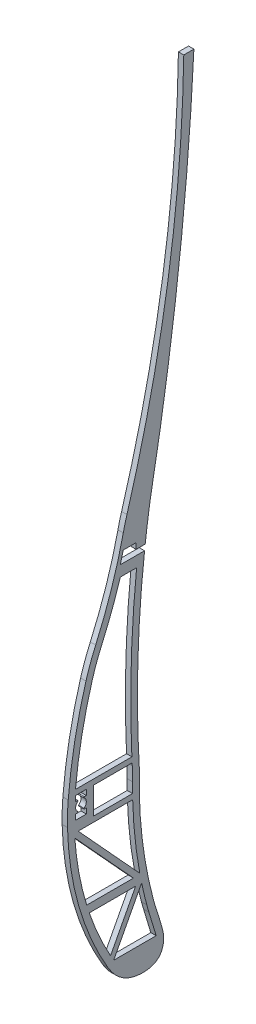
SolidWorks part; units mm, degrees
ref_plane "Front Plane" through (0, 0, 0) normal (0, 0, 1) x (1, 0, 0)
ref_plane "Top Plane" through (0, 0, 0) normal (0, 1, 0) x (1, 0, 0)
ref_plane "Right Plane" through (0, 0, 0) normal (1, 0, 0) x (0, 0, -1)
sketch "rib1" plane through (0, 0, 0) normal (1, 0, 0) x (0, 0, -1)
  line L0 (-71.2313, 530.3957) -> (928.7687, 530.3957) construction
  line L1 (884.1904, 599.9039) -> (887.9745, 599.9039)
  line L2 (856.9345, 370.6416) -> (865.0745, 370.6416)
  line L3 (850.4345, 376.6416) -> (850.4345, 379.6416)
  line L4 (850.4345, 376.6416) -> (850.4345, 373.6416)
  line L5 (840.8063, 376.6416) -> (845.8063, 376.6416) construction
  line L6 (843.8063, 376.6416) -> (843.8063, 374.6416) construction
  line L7 (843.8063, 374.6416) -> (843.8063, 372.6416)
  line L8 (855.8579, 382.6416) -> (843.7452, 382.6416)
  line L9 (855.8579, 382.6416) -> (864.8136, 382.6416)
  line L10 (856.9345, 368.6416) -> (844.7619, 368.6416)
  line L11 (856.9345, 368.6416) -> (865.1127, 368.6416)
  line L12 (866.2204, 340.1291) -> (848.917, 340.1291)
  line L13 (858.3122, 320.8088) -> (858.0269, 320.2668)
  line L14 (848.4203, 343.1291) -> (847.9481, 343.1291)
  line L15 (860.5104, 442.9155) -> (866.5886, 442.9155)
  line L16 (858.0269, 320.2668) -> (873.8862, 320.2668)
  line L17 (855.8579, 318.9992) -> (874.2194, 327.9134) construction
  line L18 (854.766, 321.2482) -> (871.1797, 329.2167) construction
  line L19 (871.1797, 329.2167) -> (873.8862, 320.2668)
  line L20 (843.5049, 367.0528) -> (865.4106, 343.1291)
  line L21 (866.2204, 340.1291) -> (856.8415, 322.3087)
  line L22 (844.7619, 368.6416) -> (867.7752, 343.5082)
  line L23 (868.4574, 340.0851) -> (858.3122, 320.8088)
  line L24 (865.4106, 343.1291) -> (848.4203, 343.1291)
  line L25 (843.8063, 372.6416) -> (847.8063, 372.6416)
  line L26 (856.9345, 370.6416) -> (850.4345, 370.6416)
  line L27 (850.4345, 370.6416) -> (850.4345, 373.6416)
  line L28 (847.8063, 372.6416) -> (847.8063, 374.6416)
  line L29 (855.8579, 380.6416) -> (864.9113, 380.6416)
  line L30 (855.8579, 380.6416) -> (850.4345, 380.6416)
  line L31 (850.4345, 380.6416) -> (850.4345, 379.6416)
  line L32 (843.8063, 374.6416) -> (844.5413, 374.6416)
  line L33 (843.8063, 378.6416) -> (843.8063, 380.6416)
  line L34 (843.8063, 380.6416) -> (847.8063, 380.6416)
  line L35 (843.8063, 378.6416) -> (844.5413, 378.6416)
  line L36 (847.8063, 380.6416) -> (847.8063, 378.6416)
  line L37 (869.548, 446.9155) -> (865.3752, 446.9155)
  line L38 (847.8063, 378.6416) -> (847.0712, 378.6416)
  line L39 (847.8063, 374.6416) -> (847.0712, 374.6416)
  line L40 (870.008, 446.9155) -> (851.9209, 446.9155) construction
  line L41 (869.7893, 448.9413) -> (866.4011, 448.9198)
  line L42 (866.4011, 448.9198) -> (866.4011, 451.1028)
  line L43 (866.4011, 451.1028) -> (861.6081, 451.1028)
  line L44 (861.6081, 451.1028) -> (860.5104, 446.9155)
  line L45 (860.5104, 446.9155) -> (865.3752, 446.9155)
  arc A0 (844.6563, 378.2779) -> (844.6563, 375.0052) centre (845.8063, 376.6416) ccw
  arc A1 (841.0443, 380.5713) -> (847.6718, 415.72) centre (1017.3451, 365.528) cw
  arc A2 (851.2954, 425.5507) -> (861.6081, 456.6454) centre (699.0135, 493.3134) ccw
  arc A3 (862.9829, 461.9026) -> (884.1904, 599.9039) centre (374.0528, 607.6697) ccw
  arc A4 (840.7788, 371.8072) -> (855.8579, 318.9992) centre (950.1899, 374.4922) ccw
  arc A5 (867.6216, 376.9662) -> (872.8022, 332.64) centre (1022.9399, 372.6533) ccw
  arc A6 (867.6216, 376.9662) -> (869.548, 446.9155) centre (1263.0251, 401.0778) cw
  arc A7 (871.9368, 463.9152) -> (887.9745, 599.9039) centre (-120.6116, 649.9108) ccw
  arc A8 (874.2194, 327.9134) -> (872.8022, 332.64) centre (950.104, 353.2418) cw
  arc A9 (841.0443, 380.5713) -> (840.7788, 371.8072) centre (920.7547, 373.7698) ccw
  arc A10 (851.2954, 425.5507) -> (847.6718, 415.72) centre (924.3857, 393.0268) ccw
  arc A11 (862.9829, 461.9026) -> (861.6081, 456.6454) centre (939.6482, 439.046) ccw
  arc A12 (871.4996, 461.3529) -> (871.9368, 463.9152) centre (950.5681, 449.1804) cw
  arc A13 (843.7452, 382.6416) -> (850.0691, 415.0108) centre (1017.3451, 365.528) cw
  arc A14 (853.5794, 424.5344) -> (850.0691, 415.0108) centre (924.3857, 393.0268) ccw
  arc A15 (853.5794, 424.5344) -> (860.5104, 442.9155) centre (699.0135, 493.3134) ccw
  arc A16 (843.5353, 380.3587) -> (850.0691, 415.0108) centre (1017.3451, 365.528) cw construction
  arc A17 (843.5049, 367.0528) -> (847.9481, 343.1291) centre (950.1899, 374.4922) ccw
  arc A18 (865.0721, 374.4641) -> (865.0745, 370.6416) centre (1022.9399, 372.6533) ccw
  arc A19 (864.962, 379.6766) -> (864.9113, 380.6416) centre (1263.0251, 401.0778) cw
  arc A20 (871.1797, 329.2167) -> (870.3865, 331.9962) centre (950.104, 353.2418) cw
  arc A21 (868.4574, 340.0851) -> (870.3865, 331.9962) centre (1022.9399, 372.6533) ccw
  arc A22 (865.3787, 461.1883) -> (886.6901, 599.8658) centre (374.0528, 607.6697) ccw construction
  arc A23 (865.1195, 376.9245) -> (870.3865, 331.9962) centre (1022.9399, 372.6533) ccw construction
  arc A24 (869.4795, 464.3757) -> (885.4776, 600.0277) centre (-120.6116, 649.9108) ccw construction
  arc A25 (843.278, 371.8685) -> (858.0127, 320.2668) centre (950.1899, 374.4922) ccw construction
  arc A26 (853.5794, 424.5344) -> (864.0469, 456.0955) centre (699.0135, 493.3134) ccw construction
  arc A27 (865.3787, 461.1883) -> (864.0469, 456.0955) centre (939.6482, 439.046) ccw construction
  arc A28 (865.1195, 376.9245) -> (869.0287, 461.7333) centre (1263.0251, 401.0778) cw construction
  arc A29 (869.0287, 461.7333) -> (869.4795, 464.3757) centre (950.5681, 449.1804) cw construction
  arc A30 (848.917, 340.1291) -> (856.8415, 322.3087) centre (950.1899, 374.4922) ccw
  arc A31 (865.1127, 368.6416) -> (867.7752, 343.5082) centre (1022.9399, 372.6533) ccw
  arc A32 (864.8136, 382.6416) -> (866.5886, 442.9155) centre (1263.0251, 401.0778) cw
  arc A33 (865.0721, 374.4641) -> (864.962, 379.6766) centre (785.0773, 375.3817) ccw
  arc A34 (844.5413, 378.6416) -> (844.6563, 378.2779) centre (844.5413, 378.4416) cw
  arc A35 (844.6563, 375.0052) -> (844.5413, 374.6416) centre (844.5413, 374.8416) cw
  arc A36 (846.9562, 375.0052) -> (846.9562, 378.2779) centre (845.8063, 376.6416) ccw
  arc A37 (847.0712, 378.6416) -> (846.9562, 378.2779) centre (847.0712, 378.4416) ccw
  arc A38 (847.0712, 374.6416) -> (846.9562, 375.0052) centre (847.0712, 374.8416) cw
  arc A39 (869.7893, 448.9413) -> (871.4996, 461.3529) centre (1263.0251, 401.0778) cw
  arc A40 (867.6216, 376.9662) -> (871.4996, 461.3529) centre (1263.0251, 401.0778) cw construction
  spline S0 degree 3 poles (855.8579, 318.9992) (859.3648, 313.0596) (867.0534, 309.8477) (875.8907, 311.5767) (877.0472, 317.8757) (875.7309, 323.2627) (874.9921, 325.5984) (874.2194, 327.9134) knots 0 0 0 0 0.275026 0.518183 0.708506 0.751927 0.952395 0.952395 0.952395 0.952395
  point P95 (843.8063, 374.6416)
  point P115 (845.8063, 374.6416)
  dimension "D2" = 2.5
  dimension "D3" = 0.2
  dimension "D4" = 0.2
  dimension "D5" = 0.2
  dimension "D6" = 0.2
  dimension "D1" = 1000
sketch "rib2" plane through (0, 0, 0) normal (1, 0, 0) x (0, 0, -1)
  line L0 (-154.4211, 376.6416) -> (49845.5789, 376.6416) construction
  line L1 (-144.1421, 380.6416) -> (49855.8579, 380.6416) construction
  line L2 (-143.0655, 370.6416) -> (49856.9345, 370.6416) construction
  line L3 (782.8933, 343.3859) -> (760.3563, 368.2109)
  line L4 (-143.0655, 368.6416) -> (49856.9345, 368.6416) construction
  line L5 (-144.1421, 382.6416) -> (49855.8579, 382.6416) construction
  line L6 (785.2354, 343.762) -> (762.6647, 368.6416)
  line L7 (764.6298, 343.3859) -> (782.8933, 343.3859)
  line L8 (783.7374, 340.3859) -> (774.2204, 321.3554)
  line L9 (767.5719, 380.6416) -> (767.5719, 370.6416)
  line L10 (767.5719, 370.6416) -> (782.7291, 370.6416)
  line L11 (767.5719, 380.6416) -> (782.2855, 380.6416)
  line L12 (765.5126, 340.3859) -> (783.7374, 340.3859)
  line L13 (762.6647, 368.6416) -> (782.7755, 368.6416)
  line L14 (776.5435, 321.5294) -> (789.8459, 321.5294)
  line L15 (760.7138, 382.6416) -> (782.1585, 382.6416)
  line L16 (770.7866, 427.4918) -> (781.8144, 427.4918)
  line L17 (801.9062, 590.4081) -> (805.115, 590.4081)
  line L18 (757.9166, 376.6416) -> (762.9166, 376.6416) construction
  line L20 (785.9296, 340.298) -> (776.5435, 321.5294)
  circle A0 centre (762.9166, 376.6416) radius 2
  arc A1 (758.9972, 388.4269) -> (758.7602, 360.0657) centre (857.8646, 373.419) ccw
  spline S0 degree 3 poles (758.7602, 360.0657) (759.4545, 354.9126) (761.6392, 342.918) (767.6025, 326.3565) (776.3644, 313.1833) (785.8807, 308.842) (791.3139, 310.6103) (793.0754, 312.9879) (793.3375, 316.1077) (791.0414, 329.6431) (787.956, 341.1966) (785.2042, 359.6207) (785.4538, 372.9971) (783.4315, 397.4301) (785.2476, 420.7625) (783.0535, 455.8097) (784.4694, 464.3867) (788.1328, 479.2935) (793.2428, 503.9805) (802.5401, 542.6054) (805.2587, 572.3941) (805.115, 590.4081) knots 0.028705 0.028705 0.028705 0.028705 0.059247 0.100348 0.1322 0.149146 0.158796 0.160734 0.16766 0.175847 0.234409 0.24607 0.285136 0.310616 0.385264 0.441942 0.454033 0.506165 0.624061 0.777474 1 1 1 1
  spline S1 degree 3 poles (801.9062, 590.4081) (801.6966, 560.1521) (794.9988, 516.4373) (781.9369, 464.9221) (769.955, 434.3358) (762.9603, 410.299) (759.9193, 394.5015) (758.9972, 388.4269) knots 0 0 0 0 0.408823 0.598513 0.719262 0.854061 0.937351 0.937351 0.937351 0.937351
  spline S2 degree 3 poles (760.3563, 368.2109) (760.6455, 365.1083) (761.2971, 359.3998) (762.6856, 351.2079) (763.8909, 346.0643) (764.604, 343.4789) (764.6298, 343.3859) knots 0.01313 0.01313 0.01313 0.01313 0.031626 0.047245 0.062864 0.063447 0.063447 0.063447 0.063447
  spline S3 degree 3 poles (765.5126, 340.3859) (765.9421, 339.0082) (767.2255, 335.1967) (769.2617, 330.2911) (771.6089, 325.6402) (773.0967, 323.06) (774.0043, 321.6748) (774.2204, 321.3554) knots 0.069751 0.069751 0.069751 0.069751 0.078483 0.094102 0.101912 0.109721 0.112105 0.112105 0.112105 0.112105
  spline S5 degree 3 poles (782.7291, 370.6416) (782.7064, 371.5634) (782.6438, 373.8426) (782.4996, 377.1608) (782.3523, 379.5799) (782.2855, 380.6416) knots 0.276245 0.276245 0.276245 0.276245 0.281529 0.289339 0.295445 0.295445 0.295445 0.295445
  spline S6 degree 3 poles (789.8459, 321.5294) (789.8142, 321.6995) (789.7504, 322.0389) (789.4577, 323.5807) (788.9295, 326.2404) (788.1496, 329.9526) (787.3325, 333.724) (786.5882, 337.1579) (786.1256, 339.3494) (785.9296, 340.298) knots 0.178918 0.178918 0.178918 0.178918 0.179894 0.18087 0.187816 0.195625 0.203435 0.211244 0.21717 0.21717 0.21717 0.21717
  spline S7 degree 3 poles (785.2354, 343.762) (784.9117, 345.4358) (784.3695, 348.4126) (783.6834, 352.846) (783.0923, 358.3507) (782.8866, 363.6197) (782.8011, 367.501) (782.7755, 368.6416) knots 0.224345 0.224345 0.224345 0.224345 0.234672 0.242482 0.250291 0.26591 0.27243 0.27243 0.27243 0.27243
  spline S8 degree 3 poles (782.1585, 382.6416) (782.0098, 384.985) (781.5323, 392.7288) (781.6016, 402.5045) (781.8121, 413.0284) (781.8895, 420.0466) (781.8563, 425.0079) (781.8229, 427.0307) (781.8144, 427.4918) knots 0.299279 0.299279 0.299279 0.299279 0.312767 0.344005 0.359624 0.375243 0.383052 0.385336 0.385336 0.385336 0.385336
  spline S9 degree 3 poles (770.7866, 427.4918) (769.4671, 423.3387) (766.9647, 414.7701) (763.3804, 399.8515) (761.5251, 389.0141) (760.7138, 382.6416) knots 0.752168 0.752168 0.752168 0.752168 0.811773 0.874217 0.962264 0.962264 0.962264 0.962264
  point P26 (765.5126, 340.3859)
  point P30 (764.6298, 343.3859)
  point P35 (774.2204, 321.3554)
  point P36 (789.8459, 321.5294)
  point P37 (785.9296, 340.298)
  point P39 (760.3563, 368.2109)
  point P40 (760.0729, 371.4986)
  dimension "D1" = 100
sketch "Sketch5" plane through (0, 0, 0) normal (1, 0, 0) x (0, 0, -1)
  line L0 (-200154.4211, 376.6416) -> (249845.5789, 376.6416) construction
  line L1 (693.317, 322.1015) -> (707.0464, 322.1015)
  line L2 (695.5696, 447.1101) -> (698.3736, 447.1101)
  line L3 (698.6642, 410.7316) -> (681.8197, 410.7316)
  line L4 (698.7261, 405.5878) -> (680.4847, 405.5878)
  line L5 (677.0801, 382.6416) -> (699.3215, 382.6416)
  line L7 (699.7026, 368.6416) -> (679.4803, 368.6416)
  line L8 (-200143.0655, 368.6416) -> (249856.9345, 368.6416) construction
  line L9 (674.1545, 376.6416) -> (679.1545, 376.6416) construction
  line L10 (684.2181, 380.6416) -> (684.2181, 370.6416)
  line L11 (-200144.1421, 380.6416) -> (249855.8579, 380.6416) construction
  line L12 (-200143.0655, 370.6416) -> (249856.9345, 370.6416) construction
  line L13 (684.2181, 370.6416) -> (699.6248, 370.6416)
  line L14 (702.2048, 368.6416) -> (702.335, 365.9116)
  line L15 (699.3639, 380.6416) -> (684.2181, 380.6416)
  line L16 (708.485, 312.754) -> (708.6651, 312.9152)
  line L17 (706.7921, 314.6987) -> (706.9599, 314.7434)
  line L18 (699.8434, 365.7077) -> (699.7071, 368.5354)
  line L19 (682.1263, 343.4207) -> (681.5591, 343.4207)
  line L20 (700.6109, 340.4181) -> (682.6985, 340.4181)
  line L21 (699.3639, 380.6416) -> (699.6248, 370.6416)
  line L22 (705.0572, 343.4207) -> (704.8181, 343.4207)
  line L23 (716.7384, 582.0418) -> (720.2752, 582.0418)
  line L24 (693.317, 322.1015) -> (702.7962, 340.2834)
  line L25 (702.2445, 343.7103) -> (679.4803, 368.6416)
  line L26 (691.5466, 323.0319) -> (700.6109, 340.4181)
  line L28 (699.8006, 343.4207) -> (682.1263, 343.4207)
  line L32 (699.8006, 343.4207) -> (677.0187, 368.3713)
  circle A0 centre (679.1545, 376.6416) radius 2
  spline S0 degree 3 poles (674.1545, 376.6416) (674.6209, 363.9047) (675.4244, 348.9718) (687.0005, 324.6734) (691.715, 318.3055) (697.5054, 311.9056) (699.9912, 310.5046) (704.8962, 310.5781) (707.1739, 311.6254) (708.485, 312.754) knots 0 0 0 0 0.082297 0.137777 0.177735 0.177735 0.194632 0.194632 0.2043 0.2043 0.2043 0.2043
  spline S1 degree 3 poles (716.7384, 582.0418) (716.9491, 569.6586) (716.384, 531.2528) (699.2016, 484.7456) (692.8166, 441.1757) (677.838, 413.403) (675.0171, 391.1698) (674.1545, 376.6416) knots 0 0 0 0 0.169562 0.555938 0.689283 0.791056 1 1 1 1
  spline S2 degree 3 poles (702.2445, 343.7103) (702.1641, 344.2407) (701.7657, 346.9448) (701.1382, 351.8745) (700.5581, 357.5193) (700.1402, 362.1447) (699.9401, 364.5255) (699.8434, 365.7077) knots 0.317112 0.317112 0.317112 0.317112 0.32289 0.346516 0.370142 0.381955 0.393768 0.393768 0.393768 0.393768
  spline S4 degree 3 poles (702.2048, 368.6416) (701.8669, 376.5926) (701.8555, 384.7425) (701.1266, 402.784) (701.1396, 431.7405) (700.5544, 456.9254) (705.1133, 487.005) (717.5576, 525.1697) (721.078, 562.1394) (720.2752, 582.0418) knots 0.402967 0.402967 0.402967 0.402967 0.483086 0.483086 0.591391 0.687653 0.687653 0.844633 1 1 1 1
  spline S5 degree 3 poles (699.3215, 382.6416) (699.3024, 383.5334) (699.2425, 386.2646) (699.1476, 389.8671) (699.0014, 393.4021) (698.878, 397.2735) (698.7899, 401.3622) (698.7401, 404.5905) (698.7261, 405.5878) knots 0.449941 0.449941 0.449941 0.449941 0.458939 0.477596 0.486925 0.496254 0.514911 0.523067 0.523067 0.523067 0.523067
  spline S6 degree 3 poles (699.7071, 368.5354) (699.7056, 368.5708) (699.7041, 368.6062) (699.7026, 368.6416) knots 0.402967 0.402967 0.402967 0.402967 0.40332 0.40332 0.40332 0.40332
  spline S7 degree 3 poles (682.6985, 340.4181) (683.0121, 339.6321) (683.9949, 337.2558) (685.7648, 333.3639) (687.9735, 329.011) (689.7493, 325.8616) (690.8989, 324.0094) (691.3927, 323.2607) (691.5466, 323.0319) knots 0.095831 0.095831 0.095831 0.095831 0.10215 0.114919 0.127687 0.140456 0.14684 0.149678 0.149678 0.149678 0.149678
  spline S8 degree 3 poles (677.0187, 368.3713) (677.0192, 368.3626) (677.0681, 367.4934) (677.2257, 364.9551) (677.5669, 360.9606) (678.1637, 356.4034) (679.0103, 351.9539) (680.1158, 347.6804) (681.0683, 344.7879) (681.5591, 343.4207) knots 0.019088 0.019088 0.019088 0.019088 0.019153 0.025537 0.038306 0.051075 0.063844 0.076612 0.087747 0.087747 0.087747 0.087747
  spline S9 degree 3 poles (708.6651, 312.9152) (709.0596, 313.2832) (711.3268, 316.9807) (705.4793, 334.2076) (703.6294, 350.0939) (702.335, 365.9116) knots 0.204759 0.204759 0.204759 0.204759 0.207895 0.236848 0.393768 0.393768 0.393768 0.393768
  spline S10 degree 3 poles (676.659, 376.6416) (676.6584, 376.6321) (676.6578, 376.6225) (676.6573, 376.613) knots 0.999862 0.999862 0.999862 0.999862 1 1 1 1
  spline S11 degree 3 poles (707.0464, 322.1015) (707.0052, 322.2371) (706.9227, 322.5094) (706.5342, 323.8003) (705.9077, 326.017) (705.0863, 329.1749) (704.0811, 333.4582) (703.3421, 337.155) (702.8797, 339.7948) (702.7962, 340.2834) knots 0.237993 0.237993 0.237993 0.237993 0.239469 0.240946 0.252011 0.263824 0.275637 0.299263 0.304623 0.304623 0.304623 0.304623
  spline S12 degree 3 poles (680.4847, 405.5878) (680.2388, 404.5378) (679.0822, 399.2686) (677.9122, 391.5905) (677.2696, 384.9533) (677.0801, 382.6416) knots 0.859357 0.859357 0.859357 0.859357 0.875 0.9375 0.970921 0.970921 0.970921 0.970921
  spline S13 degree 3 poles (698.6642, 410.7316) (698.6438, 412.7052) (698.5832, 419.5769) (698.503, 431.741) (698.3426, 441.7088) (698.3711, 446.7739) (698.3736, 447.1101) knots 0.536769 0.536769 0.536769 0.536769 0.552225 0.58954 0.626855 0.629511 0.629511 0.629511 0.629511
  spline S15 degree 3 poles (695.5696, 447.1101) (695.4451, 446.6155) (694.7557, 443.952) (693.3092, 439.1408) (690.7575, 432.8707) (687.9819, 426.8359) (685.294, 420.8884) (683.2818, 415.5566) (682.219, 412.126) (681.8197, 410.7316) knots 0.649129 0.649129 0.649129 0.649129 0.65625 0.6875 0.71875 0.75 0.78125 0.8125 0.833615 0.833615 0.833615 0.833615
sketch "Sketch6" plane through (0, 0, 0) normal (1, 0, 0) x (0, 0, -1)
  line L0 (-200154.4211, 376.6416) -> (249845.5789, 376.6416) construction
  line L1 (594.2077, 382.6416) -> (615.9917, 382.6416)
  line L2 (-200144.1421, 382.6416) -> (249855.8579, 382.6416) construction
  line L3 (617.0002, 368.6416) -> (597.1315, 368.6416)
  line L4 (-200143.0655, 368.6416) -> (249856.9345, 368.6416) construction
  line L7 (609.0006, 321.5886) -> (608.931, 321.4458)
  line L8 (610.7981, 320.7115) -> (610.2002, 319.4863)
  line L9 (594.4326, 368.6416) -> (594.0581, 368.6416)
  line L11 (594.4326, 368.6416) -> (617.3118, 343.3906)
  line L12 (618.1756, 340.3906) -> (609.0006, 321.5886)
  line L13 (597.1315, 368.6416) -> (619.7239, 343.7071)
  line L23 (620.3211, 340.2268) -> (610.7981, 320.7115)
  line L28 (618.1756, 340.3906) -> (599.7563, 340.3906)
  line L29 (617.3118, 343.3906) -> (598.7382, 343.3906)
  arc A0 (610.8725, 452.2517) -> (615.4146, 451.3048) centre (613.0575, 451.3657) cw
  spline S0 degree 3 poles (591.4519, 376.6416) (590.8724, 355.6832) (598.0127, 330.747) (614.7237, 309.0913) (626.4002, 308.0944) (627.1878, 324.0074) (622.1741, 339.2467) (620.5135, 359.7877) (618.195, 380.0068) (618.3402, 403.8303) (616.7499, 433.3564) (618.9592, 474.5213) (631.6465, 520.1908) (636.0177, 556.3417) (635.098, 572.5915) knots 0 0 0 0 0.181753 0.211103 0.236632 0.255743 0.327686 0.385848 0.430346 0.504499 0.591378 0.686471 0.859586 1 1 1 1
  spline S1 degree 3 poles (632.3767, 572.5915) (632.331, 559.797) (630.7518, 538.4728) (623.6454, 509.5847) (617.1086, 483.6159) (609.1878, 456.4292) (602.6277, 431.1093) (594.4581, 405.0022) (591.6906, 387.7261) (591.4519, 376.6416) knots 0 0 0 0 0.191351 0.317516 0.443871 0.591483 0.740453 0.834547 1 1 1 1
  spline S2 degree 3 poles (619.7239, 343.7071) (619.5881, 344.5842) (619.2022, 347.2732) (618.6764, 351.7986) (618.1443, 357.2765) (617.6179, 362.6875) (617.2186, 366.4692) (617.0187, 368.4566) (617.0002, 368.6416) knots 0.33611 0.33611 0.33611 0.33611 0.343735 0.359361 0.374986 0.390612 0.406237 0.40784 0.40784 0.40784 0.40784
  spline S3 degree 3 poles (599.7563, 340.3906) (599.7882, 340.3011) (600.4188, 338.5434) (601.7436, 335.154) (603.9399, 330.3213) (606.3333, 325.742) (608.0626, 322.8243) (608.931, 321.4458) knots 0.108518 0.108518 0.108518 0.108518 0.109355 0.124981 0.140606 0.156231 0.170688 0.170688 0.170688 0.170688
  spline S4 degree 3 poles (610.8725, 452.2517) (610.269, 449.893) (608.8998, 444.6758) (606.7371, 436.6294) (604.5222, 428.0779) (602.3578, 419.4861) (600.0573, 410.8763) (597.5945, 402.3898) (595.6103, 393.891) (594.6157, 387.2692) (594.2744, 383.5122) (594.2077, 382.6416) knots 0.448611 0.448611 0.448611 0.448611 0.500019 0.562521 0.625024 0.687526 0.750029 0.812531 0.875033 0.937536 0.956374 0.956374 0.956374 0.956374
  spline S5 degree 3 poles (594.0581, 368.6416) (594.1057, 367.7673) (594.4036, 363.3735) (595.4715, 355.4692) (597.3077, 347.9625) (598.5477, 343.9825) (598.7382, 343.3906) knots 0.023466 0.023466 0.023466 0.023466 0.031229 0.062479 0.09373 0.09921 0.09921 0.09921 0.09921
  spline S6 degree 3 poles (610.2002, 319.4863) (610.3292, 319.2923) (610.9476, 318.3692) (612.075, 316.7416) (613.5938, 314.8775) (615.268, 313.3623) (617.1903, 312.2288) (619.6971, 311.4612) (621.7209, 311.3604) (622.8414, 311.5923) (623.3355, 311.851) (623.4973, 312.0037) (623.7734, 312.4798) (624.0122, 313.3728) (624.1915, 314.9548) (624.1754, 317.4057) (624.0268, 320.2009) (623.7469, 322.9038) (623.3647, 325.5305) (622.9006, 328.1059) (622.2032, 331.5008) (621.2956, 335.4836) (620.6086, 338.7108) (620.3211, 340.2268) knots 0.177597 0.177597 0.177597 0.177597 0.179669 0.187482 0.195295 0.203107 0.21092 0.218733 0.226545 0.230452 0.234358 0.238264 0.242171 0.246077 0.249983 0.257796 0.265609 0.273421 0.281234 0.289047 0.296859 0.312485 0.325931 0.325931 0.325931 0.325931
  spline S7 degree 3 poles (615.9917, 382.6416) (615.8973, 385.0577) (615.7504, 391.1062) (615.6642, 400.7347) (615.3415, 411.5075) (614.9499, 422.3472) (614.7472, 433.2494) (614.9316, 442.9184) (615.2536, 448.9371) (615.4146, 451.3048) knots 0.447995 0.447995 0.447995 0.447995 0.468738 0.499989 0.53124 0.56249 0.593741 0.624992 0.645293 0.645293 0.645293 0.645293
extrude "Boss-Extrude3" add sketch "rib1" along normal blind 2
equation "\"1000mmm\"=767.321"
